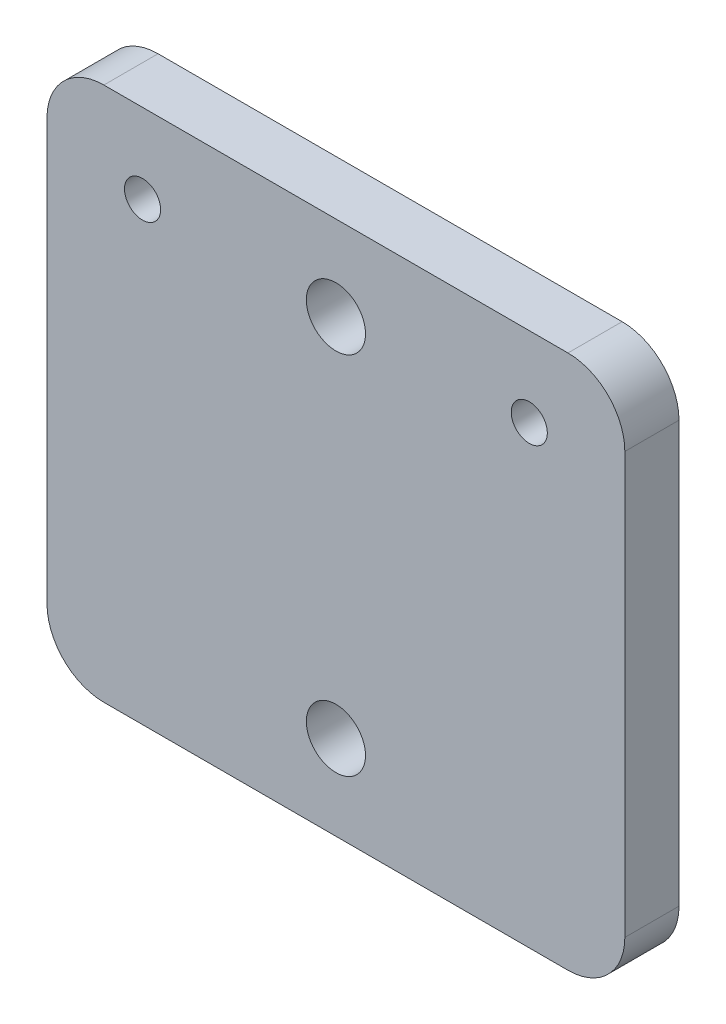
SolidWorks part; units mm, degrees
material "Aleación 6061"
ref_plane "Alzado" through (0, 0, 0) normal (0, 0, 1) x (1, 0, 0)
ref_plane "Planta" through (0, 0, 0) normal (0, 1, 0) x (1, 0, 0)
ref_plane "Vista lateral" through (0, 0, 0) normal (1, 0, 0) x (0, 0, -1)
sketch "Croquis1" plane through (0, 0, 0) normal (0, 0, 1) x (1, 0, 0)
  line L1 (0, 0) -> (50.8, 0)
  line L2 (0, 0) -> (0, 47)
  line L3 (0, 47) -> (50.8, 47)
  line L4 (50.8, 0) -> (50.8, 47)
  dimension "D1" = 47
  dimension "D2" = 50.8
extrude "Saliente-Extruir1" add sketch "Croquis1" along normal blind 4.7625
sketch "Croquis4" plane through (0, 0, 4.7625) normal (0, 0, 1) x (1, 0, 0)
  line L0 (25.4, 39.55) -> (25.4, 7.45) construction
  line L1 (0, 47) -> (0, 0) construction
  line L2 (50.8, 47) -> (0, 47) construction
  circle A0 centre (25.4, 39.55) radius 2.6
  circle A1 centre (25.4, 7.45) radius 2.6
  point P5 (25.4, 23.5)
  point P8 (0, 23.5)
  point P11 (25.4, 47)
  dimension "D1" = 5.2
  dimension "D2" = 5.2
  dimension "D3" = 37.3
extrude "Cortar-Extruir2" cut sketch "Croquis4" against normal through all
sketch "Croquis5" plane through (0, 0, 4.7625) normal (0, 0, 1) x (1, 0, 0)
  line L0 (9.25, 25.5) -> (41.55, 25.5) construction
  line L1 (0, 0) -> (50.8, 0) construction
  line L3 (50.8, 47) -> (0, 47) construction
  circle A0 centre (9.25, 25.5) radius 2.6
  circle A1 centre (41.55, 25.5) radius 2.6
  point P4 (25.4, 25.5)
  point P7 (25.4, 0)
  dimension "D2" = 5.2
  dimension "D3" = 5.2
  dimension "D1" = 37.5
  dimension "D4" = 21.5
fillet "Redondeo1" radius 5 4 edges at (0, 0, 2.3813) (50.8, 0, 2.3813) (50.8, 47, 2.3813) (0, 47, 2.3813)
sketch "Croquis7" plane through (0, 0, 4.7625) normal (0, 0, 1) x (1, 0, 0)
  line L0 (8.4, 40) -> (42.4, 40) construction
  line L3 (45.8, 47) -> (5, 47) construction
  circle A0 centre (8.4, 40) radius 1.5875
  circle A1 centre (42.4, 40) radius 1.5875
  point P4 (25.4, 40)
  point P8 (25.4, 47)
  dimension "D2" = 3.175
  dimension "D1" = 34
extrude "Cortar-Extruir5" cut sketch "Croquis7" against normal blind 10
